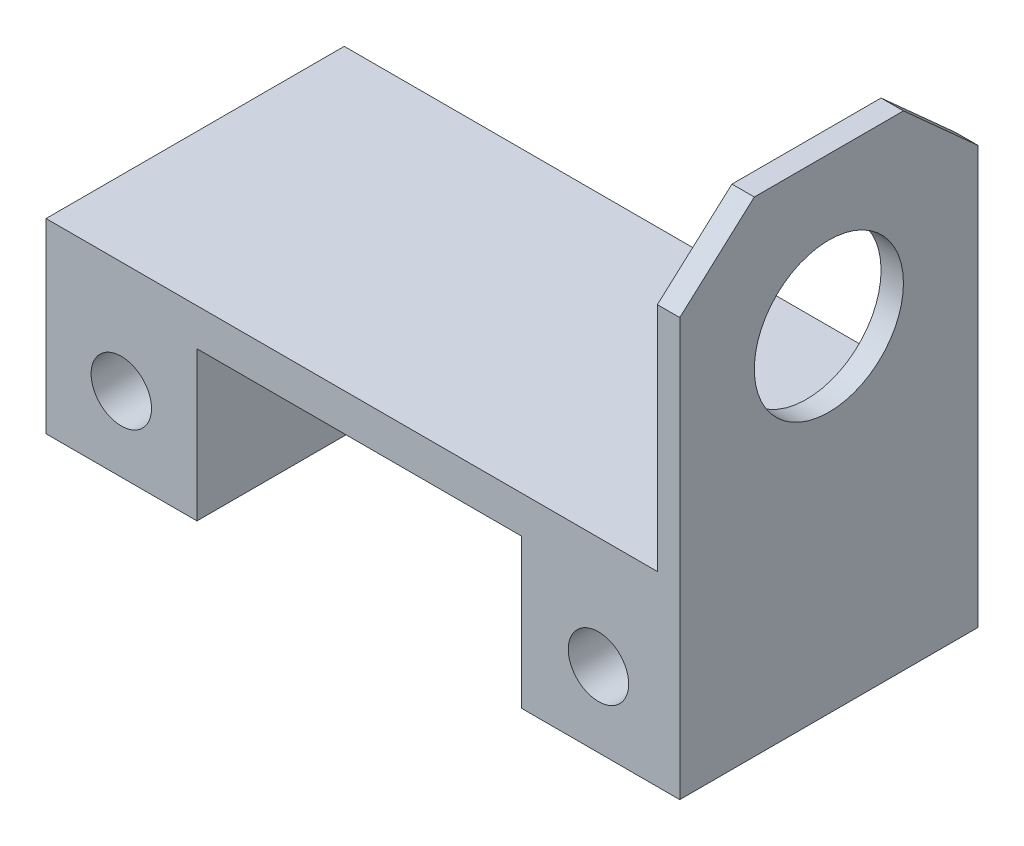
SolidWorks part; units mm, degrees
material "6063-T4"
ref_plane "Alzado" through (0, 0, 0) normal (0, 0, 1) x (1, 0, 0)
ref_plane "Planta" through (0, 0, 0) normal (0, 1, 0) x (1, 0, 0)
ref_plane "Vista lateral" through (0, 0, 0) normal (1, 0, 0) x (0, 0, -1)
sketch "Croquis1" plane through (0, 0, 0) normal (0, 0, 1) x (1, 0, 0)
  line L1 (-42, 12.5) -> (42, 12.5)
  line L2 (-42, 12.5) -> (-42, -12.5)
  line L3 (-42, -12.5) -> (42, -12.5)
  line L4 (42, 12.5) -> (42, -12.5)
  line L5 (-42, 12.5) -> (42, -12.5) construction
  line L6 (-42, -12.5) -> (42, 12.5) construction
  line L7 (-21.75, -12.5) -> (21.75, -12.5)
  line L8 (-21.75, -12.5) -> (-21.75, 7.5)
  line L9 (-21.75, 7.5) -> (21.75, 7.5)
  line L10 (21.75, -12.5) -> (21.75, 7.5)
  circle A0 centre (-31.9022, -2.5) radius 4.05
  circle A1 centre (32.0978, -2.5) radius 4.05
  point P0 (0, 0)
  dimension "D3" = 8.1
  dimension "D1" = 25
  dimension "D2" = 84
  dimension "D4" = 64
  dimension "D5" = 32
  dimension "D6" = 43.5
  dimension "D7" = 21.75
  dimension "D8" = 20
  dimension "D9" = 10
extrude "Saliente-Extruir2" add sketch "Croquis1" against normal blind 40 contours L10 L3 L4 L1 L2 L8 L9 A1 A0
ref_plane "Plano1" through (40, 0, 0) normal (1, 0, 0) x (0, 0, -1)
sketch "Croquis3" plane through (40, 0, 0) normal (1, 0, 0) x (0, 0, -1)
  line L0 (10, 52.5) -> (0, 43.5)
  line L1 (0, -12.5) -> (40, -12.5)
  line L2 (0, -12.5) -> (0, 43.5)
  line L3 (10, 52.5) -> (30, 52.5)
  line L4 (40, -12.5) -> (40, 43.5)
  line L6 (30, 52.5) -> (10, 52.5)
  line L10 (30, 52.5) -> (40, 43.5)
  point P1 (20, 52.5)
  point P2 (20, -12.5)
  dimension "D1" = 40
  dimension "D2" = 65
  dimension "D3" = 20
  dimension "D4" = 9
extrude "Saliente-Extruir3" add sketch "Croquis3" along normal blind 3 contours L10 L3 L0 L2 L1 L4
sketch "Croquis4" plane through (43, 0, 0) normal (1, 0, 0) x (0, 0, -1)
  line L0 (10, 52.5) -> (30, 52.5) construction
  line L1 (0, -12.5) -> (40, -12.5) construction
  circle A0 centre (20, 32.5) radius 10
  point P8 (20, -12.5)
  dimension "D1" = 20
  dimension "D2" = 20
extrude "Cortar-Extruir2" cut sketch "Croquis4" against normal through all
